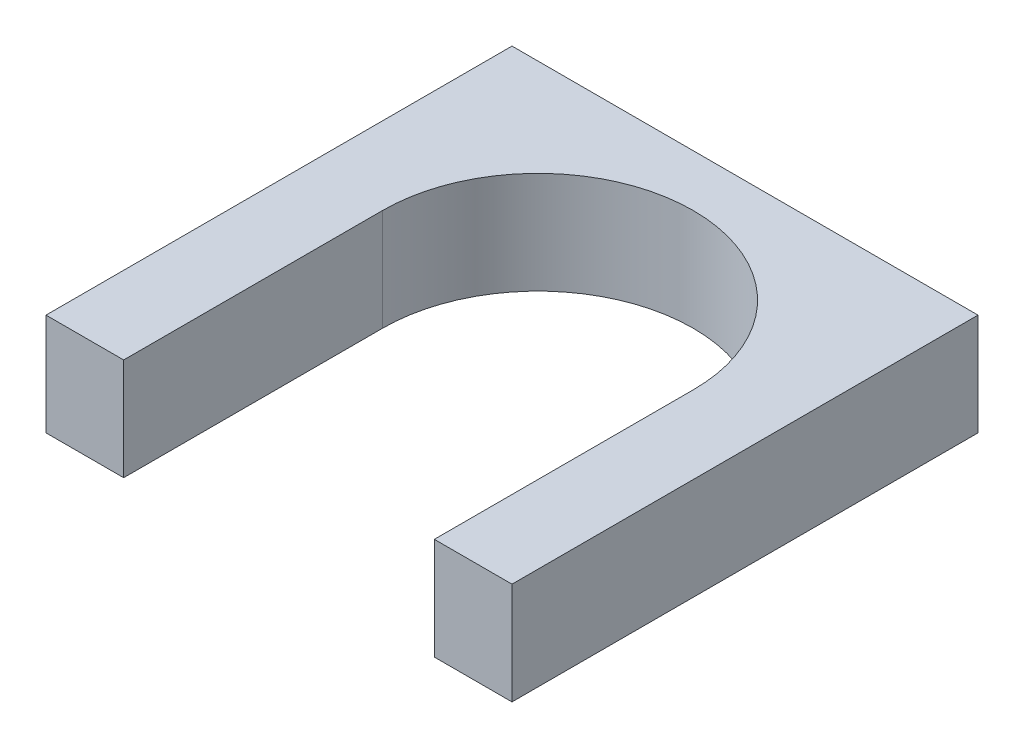
SolidWorks part; units mm, degrees
ref_plane "Plan de face" through (0, 0, 0) normal (0, 0, 1) x (1, 0, 0)
ref_plane "Plan de dessus" through (0, 0, 0) normal (0, 1, 0) x (1, 0, 0)
ref_plane "Plan de droite" through (0, 0, 0) normal (1, 0, 0) x (0, 0, -1)
sketch "Esquisse1" plane through (0, 0, 0) normal (0, 0, 1) x (1, 0, 0)
  line L0 (-49.1019, 0) -> (40.8981, 0)
  line L1 (-49.1019, 0) -> (-49.1019, 19.7)
  line L2 (-49.1019, 19.7) -> (40.8981, 19.7)
  line L3 (40.8981, 19.7) -> (40.8981, 0)
  dimension "D1" = 90
  dimension "D2" = 19.7
extrude "Boss.-Extru.1" add sketch "Esquisse1" along normal blind 90
sketch "Esquisse2" plane through (0, 19.7, 0) normal (0, 1, 0) x (1, 0, 0)
  line L0 (-49.1019, 0) -> (40.8981, -90) construction
  line L1 (-49.1019, -90) -> (40.8981, 0) construction
  line L6 (-49.1019, -40) -> (40.8981, -40) construction
  line L7 (-49.1019, -90) -> (-49.1019, 0) construction
  line L8 (40.8981, -90) -> (40.8981, 0) construction
  line L9 (40.8981, 0) -> (-49.1019, 0) construction
  line L10 (-34.1019, -40) -> (-34.1019, -90)
  line L11 (40.8981, -90) -> (-49.1019, -90) construction
  line L12 (-34.1019, -90) -> (25.8981, -90)
  line L13 (25.8981, -90) -> (25.8981, -40)
  arc A1 (25.8981, -40) -> (-34.1019, -40) centre (-4.1019, -40) ccw
  dimension "D1" = 40
  dimension "D2" = 60
extrude "Enlèv. mat.-Extru.1" cut sketch "Esquisse2" against normal blind 30
